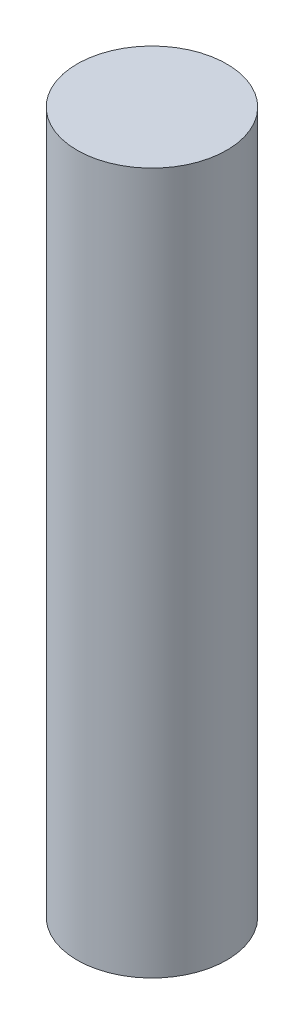
SolidWorks part; units mm, degrees
ref_plane "前基準面" through (0, 0, 0) normal (0, 0, 1) x (1, 0, 0)
ref_plane "上基準面" through (0, 0, 0) normal (0, 1, 0) x (1, 0, 0)
ref_plane "右基準面" through (0, 0, 0) normal (1, 0, 0) x (0, 0, -1)
sketch "草圖1" plane through (0, 0, 0) normal (0, 1, 0) x (1, 0, 0)
  circle A0 centre (0, 0) radius 1.6
  dimension "D1" = 3.2
extrude "填料-伸長1" add sketch "草圖1" along normal blind 15
